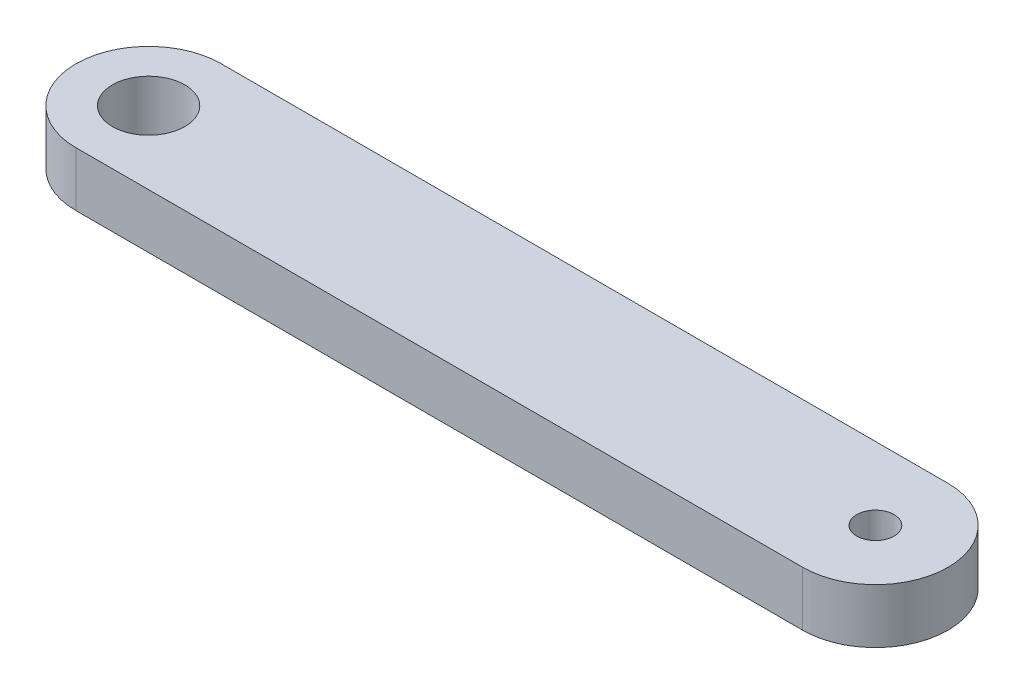
SolidWorks part; units mm, degrees
material "6061-T6 (SS)"
ref_plane "Front Plane" through (0, 0, 0) normal (0, 0, 1) x (1, 0, 0)
ref_plane "Top Plane" through (0, 0, 0) normal (0, 1, 0) x (1, 0, 0)
ref_plane "Right Plane" through (0, 0, 0) normal (1, 0, 0) x (0, 0, -1)
sketch "Sketch1" plane through (0, 0, 0) normal (0, 1, 0) x (1, 0, 0)
  line L0 (-63.5, 0) -> (0, 0) construction
  line L1 (-63.5, 6.35) -> (0, 6.35)
  line L2 (-63.5, -6.35) -> (0, -6.35)
  arc A0 (-63.5, 6.35) -> (-63.5, -6.35) centre (-63.5, 0) ccw
  arc A1 (0, -6.35) -> (0, 6.35) centre (0, 0) ccw
  point P2 (-31.75, 0)
  point P9 (-69.85, 0)
  point P10 (6.35, 0)
  dimension "D2" = 76.2
  dimension "D1" = 12.7
extrude "Boss-Extrude2" add sketch "Sketch1" along normal blind 4.7625
hole_wizard "#4 Clearance Hole1" positions "Sketch2" profile "Sketch4" hole size "#4" standard "ANSI Inch" end condition through all
sketch "Sketch2" plane through (0, 4.7625, 0) normal (0, 1, 0) x (1, 0, 0)
  point P0 (0, 0)
sketch "Sketch4" plane through (0, 4.7625, 0) normal (1, 0, 0) x (0, 0, 1)
  line L0 (0, 0) -> (0, 4.7625)
  line L1 (0, 4.7625) -> (1.6319, 4.7625)
  line L2 (1.6319, 4.7625) -> (1.6319, 0)
  line L5 (1.6319, 0) -> (0, 0)
  line L11 (0, -6.35) -> (0, 107.95) construction
  dimension "Thru Hole Dia." = 3.2639
  dimension "Thru Hole Depth" = 4.7625
sketch "Sketch5" plane through (0, 4.7625, 0) normal (0, 1, 0) x (1, 0, 0)
  circle A0 centre (-63.5, 0) radius 3.1623
  dimension "D1" = 6.3246
extrude "Cut-Extrude1" cut sketch "Sketch5" against normal through all
